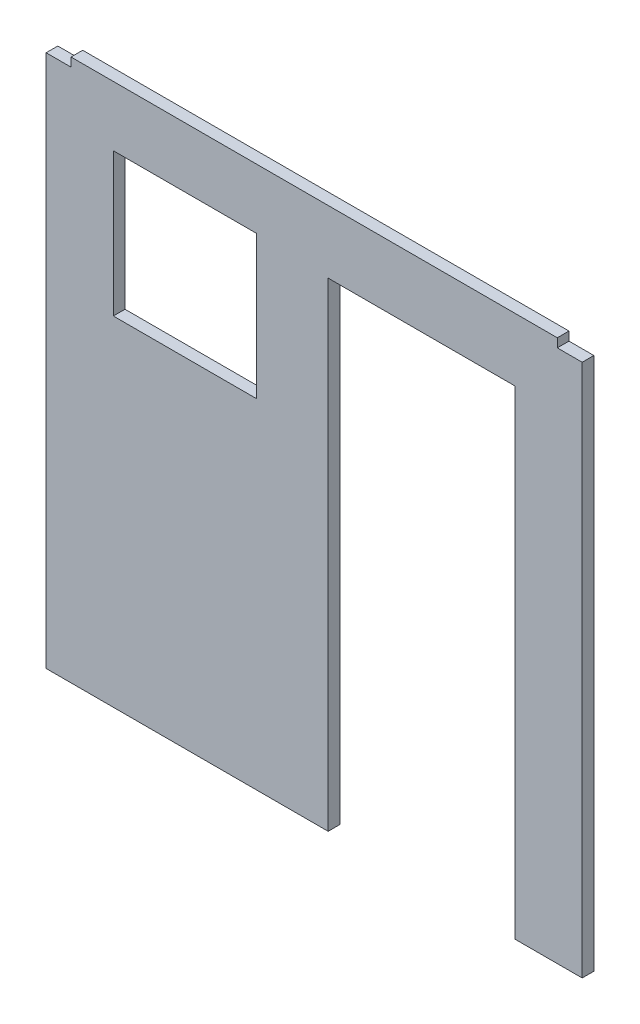
SolidWorks part; units mm, degrees
material "Polyurethane Foam Rigid"
ref_plane "Front Plane" through (0, 0, 0) normal (0, 0, 1) x (1, 0, 0)
ref_plane "Top Plane" through (0, 0, 0) normal (0, 1, 0) x (1, 0, 0)
ref_plane "Right Plane" through (0, 0, 0) normal (1, 0, 0) x (0, 0, -1)
sketch "Sketch1" plane through (0, 0, 0) normal (0, 0, 1) x (1, 0, 0)
  line L1 (-1165.225, 1178.179) -> (1165.225, 1178.179)
  line L2 (-1165.225, 1178.179) -> (-1165.225, -1178.179)
  line L3 (-1165.225, -1178.179) -> (1165.225, -1178.179)
  line L4 (1165.225, 1178.179) -> (1165.225, -1178.179)
  line L5 (-1165.225, 1178.179) -> (1165.225, -1178.179) construction
  line L6 (-1165.225, -1178.179) -> (1165.225, 1178.179) construction
  line L7 (-1165.225, 1178.179) -> (-1057.021, 1178.179)
  line L8 (-1165.225, 1178.179) -> (-1165.225, 1140.079)
  line L9 (-1165.225, 1140.079) -> (-1057.021, 1140.079)
  line L10 (-1057.021, 1178.179) -> (-1057.021, 1140.079)
  line L11 (-1165.225, 1178.179) -> (-1057.021, 1140.079) construction
  line L12 (-1165.225, 1140.079) -> (-1057.021, 1178.179) construction
  line L13 (1057.021, 1178.179) -> (1165.225, 1178.179)
  line L14 (1057.021, 1178.179) -> (1057.021, 1140.079)
  line L15 (1057.021, 1140.079) -> (1165.225, 1140.079)
  line L16 (1165.225, 1178.179) -> (1165.225, 1140.079)
  line L17 (1057.021, 1178.179) -> (1165.225, 1140.079) construction
  line L18 (1057.021, 1140.079) -> (1165.225, 1178.179) construction
  point P0 (0, 0)
  point P6 (-1111.123, 1159.129)
  point P11 (1111.123, 1159.129)
  dimension "D1" = 2330.45
  dimension "D2" = 2356.358
  dimension "D3" = 108.204
  dimension "D4" = 108.204
  dimension "D5" = 38.1
extrude "Boss-Extrude1" add sketch "Sketch1" along normal blind 50.8 contours L15 L14 L1 L10 L9 L2 L3 L4
sketch "Sketch2" plane through (0, 0, 50.8) normal (0, 0, 1) x (1, 0, 0)
  line L0 (-1165.225, -1178.179) -> (1165.225, -1178.179) construction
  line L1 (-873.125, 917.321) -> (-250.825, 917.321)
  line L2 (-873.125, 917.321) -> (-873.125, 295.021)
  line L3 (-873.125, 295.021) -> (-250.825, 295.021)
  line L4 (-250.825, 917.321) -> (-250.825, 295.021)
  line L5 (-873.125, 917.321) -> (-250.825, 295.021) construction
  line L6 (-873.125, 295.021) -> (-250.825, 917.321) construction
  line L7 (-1165.225, 1140.079) -> (-1165.225, -1178.179) construction
  line L8 (1165.225, 1140.079) -> (1165.225, -1178.179) construction
  line L9 (60.833, 904.621) -> (873.633, 904.621)
  line L10 (60.833, 904.621) -> (60.833, -1178.179)
  line L11 (60.833, -1178.179) -> (873.633, -1178.179)
  line L12 (873.633, 904.621) -> (873.633, -1178.179)
  line L13 (60.833, 904.621) -> (873.633, -1178.179) construction
  line L14 (60.833, -1178.179) -> (873.633, 904.621) construction
  point P0 (-561.975, 606.171)
  point P9 (467.233, -136.779)
  dimension "D1" = 622.3
  dimension "D2" = 622.3
  dimension "D3" = 1473.2
  dimension "D4" = 292.1
  dimension "D5" = 2082.8
  dimension "D6" = 812.8
  dimension "D7" = 291.592
extrude "Cut-Extrude1" cut sketch "Sketch2" against normal up to surface (50.8 mm away) up to face at (0, 570.0395, 0)
